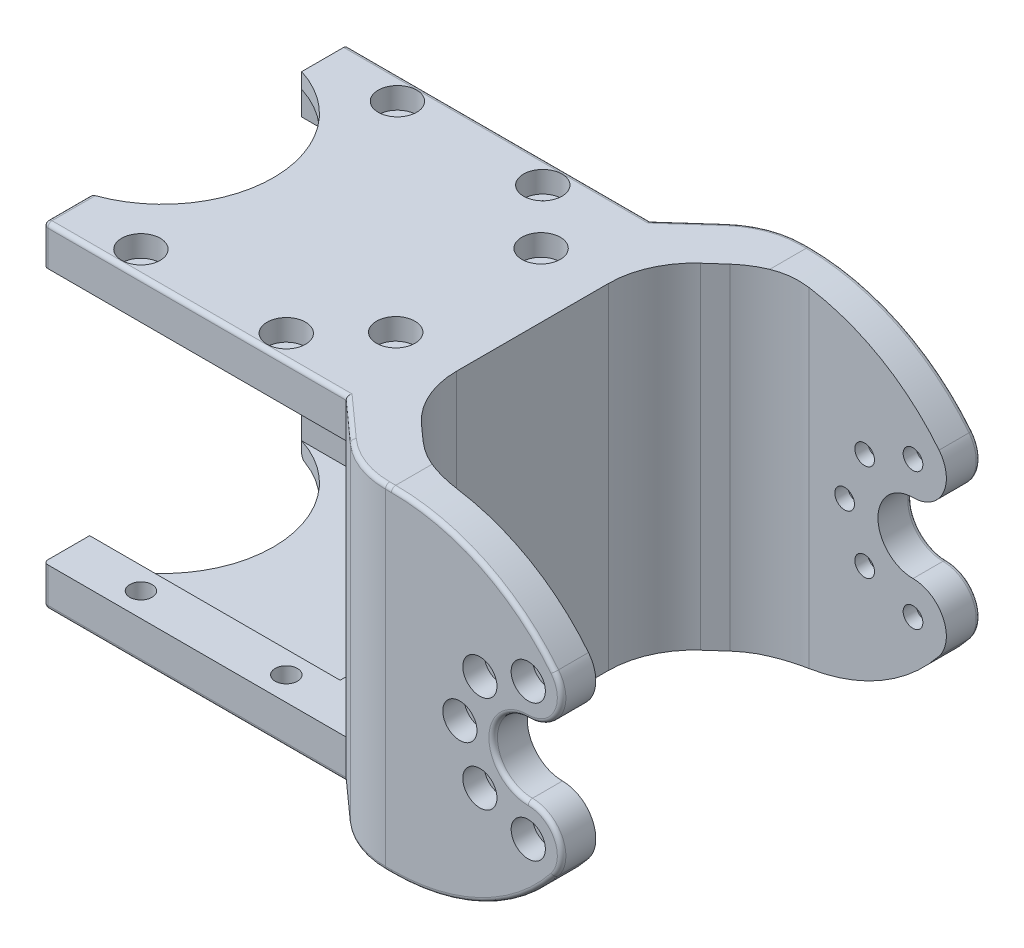
SolidWorks part; units mm, degrees
ref_plane "Front Plane" through (0, 0, 0) normal (0, 0, 1) x (1, 0, 0)
ref_plane "Top Plane" through (0, 0, 0) normal (0, 1, 0) x (1, 0, 0)
ref_plane "Right Plane" through (0, 0, 0) normal (1, 0, 0) x (0, 0, -1)
sketch "Sketch1" plane through (0, 0, 0) normal (0, 1, 0) x (1, 0, 0)
  line L0 (0, 0) -> (0, 15) construction
  line L1 (0, 15) -> (-4.5, 15) construction
  line L2 (0, 0) -> (12.5, 0) construction
  line L3 (-4.5, 12.4) -> (33.2, 12.4) construction
  line L4 (33.2, 12.4) -> (33.2, -12.4)
  line L5 (-4.5, 17.8) -> (38.3, 17.8) construction
  line L6 (38.3, 17.8) -> (38.3, -17.8)
  line L7 (33.2, 0) -> (38.3, 0) construction
  line L8 (-4.5, -12.4) -> (33.2, -12.4) construction
  line L9 (-4.5, -17.8) -> (38.3, -17.8) construction
  line L10 (-4.5, 17.8) -> (-12.2, 17.8) construction
  line L12 (-12.2, 12.4) -> (-4.5, 12.4) construction
  line L13 (-12.2, -12.4) -> (-4.5, -12.4) construction
  line L16 (-12.2, 12.4) -> (-12.2, -12.4) construction
  line L26 (3.9038, 12.4) -> (3.9038, 17.8)
  line L27 (3.9038, 17.8) -> (38.3, 17.8)
  line L28 (3.9038, -12.4) -> (3.9038, -17.8)
  line L29 (3.9038, -17.8) -> (38.3, -17.8)
  line L30 (3.9038, 12.4) -> (33.2, 12.4)
  line L31 (3.9038, -12.4) -> (33.2, -12.4)
  circle A0 centre (-4.5, 15) radius 1.3 construction
  circle A1 centre (12.5, 15) radius 1.3
  circle A2 centre (29.5, 15) radius 1.3
  circle A4 centre (29.5, -15) radius 1.3
  circle A5 centre (12.5, -15) radius 1.3
  circle A6 centre (-4.5, -15) radius 1.3 construction
  circle A8 centre (0, 0) radius 11 construction
  circle A9 centre (-4.5, 15) radius 2.25 construction
  arc A14 (3.9038, 12.4) -> (3.9038, -12.4) centre (0, 0) cw construction
  circle A15 centre (35.8, -8.5) radius 1.3
  circle A16 centre (35.8, 8.5) radius 1.3
  dimension "D4" = 2.6
  dimension "D12" = 22
  dimension "D13" = 4.5
  dimension "D16" = 6.5
  dimension "D15" = 6.3
  dimension "D14" = 13
  dimension "D1" = 15
  dimension "D2" = 4.5
  dimension "D3" = 17
  dimension "D6" = 2.6
  dimension "D7" = 34
  dimension "D8" = 3.7
  dimension "D9" = 2.8
  dimension "D10" = 5.1
  dimension "D11" = 7.7
  dimension "D5" = 3
extrude "Boss-Extrude1" add sketch "Sketch1" along normal blind 2.8
sketch "Sketch2" plane through (0, 2.8, 0) normal (0, 1, 0) x (1, 0, 0)
  line L0 (3.9038, -12.4) -> (3.9038, -17.8) construction
  line L1 (3.9038, -17.8) -> (38.3, -17.8) construction
  line L2 (38.3, 17.8) -> (38.3, -17.8) construction
  line L3 (3.9038, 17.8) -> (38.3, 17.8) construction
  line L4 (3.9038, 12.4) -> (3.9038, 17.8) construction
  line L5 (3.9038, -12.4) -> (3.9038, -17.8)
  line L6 (3.9038, -17.8) -> (38.3, -17.8)
  line L7 (38.3, 17.8) -> (38.3, -17.8)
  line L8 (3.9038, 17.8) -> (38.3, 17.8)
  line L9 (3.9038, 12.4) -> (3.9038, 17.8)
  arc A0 (3.9038, -12.4) -> (3.9038, 12.4) centre (0, 0) ccw construction
  arc A1 (3.9038, -12.4) -> (3.9038, 12.4) centre (0, 0) ccw
  circle A2 centre (12.5, -15) radius 1.3 construction
  circle A3 centre (29.5, -15) radius 1.3 construction
  circle A4 centre (35.8, -8.5) radius 1.3 construction
  circle A5 centre (35.8, 8.5) radius 1.3 construction
  circle A6 centre (29.5, 15) radius 1.3 construction
  circle A7 centre (12.5, 15) radius 1.3 construction
  circle A8 centre (12.5, -15) radius 1.3
  circle A9 centre (29.5, -15) radius 1.3
  circle A10 centre (35.8, -8.5) radius 1.3
  circle A11 centre (35.8, 8.5) radius 1.3
  circle A12 centre (29.5, 15) radius 1.3
  circle A13 centre (12.5, 15) radius 1.3
extrude "Boss-Extrude2" add sketch "Sketch2" along normal blind 1.8
sketch "Sketch3" plane through (0, 4.6, 0) normal (0, 1, 0) x (1, 0, 0)
  line L0 (0, 0) -> (38.3, 0) construction
  line L1 (38.3, -17.8) -> (38.3, 17.8) construction
  circle A0 centre (35.8, 8.5) radius 1.3 construction
  circle A1 centre (29.5, 15) radius 1.3 construction
  circle A2 centre (12.5, 15) radius 1.3 construction
  circle A3 centre (35.8, 8.5) radius 1.3 construction
  circle A4 centre (29.5, 15) radius 1.3 construction
  circle A5 centre (12.5, 15) radius 1.3 construction
  circle A6 centre (12.5, 15) radius 2.25
  circle A7 centre (29.5, 15) radius 2.25
  circle A8 centre (35.8, 8.5) radius 2.25
  circle A9 centre (35.8, -8.5) radius 2.25
  circle A10 centre (29.5, -15) radius 2.25
  circle A11 centre (12.5, -15) radius 2.25
  dimension "D1" = 4.5
extrude "Cut-Extrude1" cut sketch "Sketch3" against normal blind 2.5
sketch "Sketch4" plane through (38.3, 0, 0) normal (1, 0, 0) x (0, 0, -1)
  line L4 (-17.8, 0) -> (17.8, 0)
  line L5 (17.8, 0) -> (17.8, 4.6)
  line L6 (17.8, 4.6) -> (-17.8, 4.6)
  line L7 (-17.8, 4.6) -> (-17.8, 0)
  line L8 (-17.8, 0) -> (17.8, 0)
  line L9 (17.8, 0) -> (17.8, 4.6)
  line L10 (17.8, 4.6) -> (-17.8, 4.6)
  line L11 (-17.8, 4.6) -> (-17.8, 0)
  dimension "D1" = 0
extrude "Boss-Extrude3" add sketch "Sketch4" along normal blind 5
sketch "Sketch5" plane through (0, 0, 0) normal (0, -1, 0) x (1, 0, 0)
  line L0 (43.3, -17.8) -> (3.9038, -17.8) construction
  line L1 (43.3, 17.8) -> (39.3, 17.8)
  line L2 (43.3, 17.8) -> (43.3, -17.8)
  line L3 (43.3, -17.8) -> (39.3, -17.8)
  line L4 (39.3, 17.8) -> (39.3, -17.8)
  dimension "D1" = 4
extrude "Boss-Extrude4" add sketch "Sketch5" along normal blind 15
mirror "Mirror1" about plane through (0, -15, 0) normal (0, 1, 0) of bodies 133
sketch "Sketch6" plane through (0, 0, 0) normal (0, 0, 1) x (1, 0, 0)
  line L0 (43.3, -15) -> (67.3, -15) construction
  line L1 (43.3, 4.6) -> (43.3, -34.6) construction
  line L2 (0, 0) -> (0, -15) construction
  line L3 (0, -15) -> (43.3, -15) construction
  dimension "D1" = 24
ref_plane "Plane1" through (0, -15, 0) normal (0, 1, 0) x (1, 0, 0)
sketch "Sketch7" plane through (0, -15, 0) normal (0, 1, 0) x (1, 0, 0)
  line L0 (43.3, 0) -> (67.3, 0) construction
  line L1 (43.3, 0) -> (67.3, 0) construction
  line L2 (67.3, -20.5) -> (67.3, 20.5) construction
  point P5 (67.3, 0)
  dimension "D1" = 41
ref_plane "Plane2" through (0, 0, 20.5) normal (0, 0, 1) x (1, 0, 0)
sketch "Sketch8" plane through (0, 0, 20.5) normal (0, 0, 1) x (1, 0, 0)
  line L0 (43.3, -15) -> (67.3, -15) construction
  line L1 (51.3, -34.6) -> (51.3, 4.6)
  line L3 (43.3, 4.6) -> (43.3, -34.6) construction
  line L4 (43.3, 4.6) -> (43.3, -34.6) construction
  line L5 (43.3, -15) -> (67.3, -15) construction
  circle A0 centre (67.3, -15) radius 4.1 construction
  circle A1 centre (67.3, -7) radius 1.15
  circle A2 centre (61.6431, -9.3431) radius 1.15
  circle A3 centre (59.3, -15) radius 1.15
  circle A4 centre (61.6431, -20.6569) radius 1.15
  circle A5 centre (67.3, -23) radius 1.15
  arc A6 (67.3, -10.9) -> (67.3, -19.1) centre (67.3, -15) ccw
  arc A7 (67.3, -10.9) -> (70.3479, -4.5668) centre (67.3, -7) ccw
  arc A8 (51.3, 4.6) -> (70.3479, -4.5668) centre (51.3, -19.7734) cw
  arc A9 (67.3, -19.1) -> (70.3479, -25.4332) centre (67.3, -23) cw
  arc A10 (51.3, -34.6) -> (70.3479, -25.4332) centre (51.3, -10.2266) ccw
  point P15 (67.3, -15)
  point P22 (51.3, -15)
  dimension "D1" = 8.2
  dimension "D3" = 2.3
  dimension "D2" = 8
  dimension "D5" = 16
  dimension "D4" = 5
extrude "Boss-Extrude5" add sketch "Sketch8" along normal blind 4 separate body
sketch "Sketch10" plane through (0, 0, 17.8) normal (0, 0, 1) x (1, 0, 0)
  line L0 (39.3, -30) -> (39.3, 0) construction
  line L1 (39.3, -30) -> (39.3, 0) construction
  line L2 (3.9038, -34.6) -> (43.3, -34.6) construction
  line L3 (43.3, 4.6) -> (39.3, 4.6)
  line L4 (43.3, 4.6) -> (43.3, -34.6)
  line L5 (43.3, -34.6) -> (39.3, -34.6)
  line L6 (39.3, 4.6) -> (39.3, -34.6)
sketch "Sketch11" plane through (0, 4.6, 0) normal (0, 1, 0) x (1, 0, 0)
  line L0 (43.3, -13.3343) -> (39.3, -17.8)
  line L1 (43.3, 17.8) -> (43.3, -17.8) construction
  line L2 (3.9038, -17.8) -> (43.3, -17.8) construction
  line L3 (43.3, -13.3343) -> (51.3, -20.5)
  line L4 (39.3, -17.8) -> (46.7801, -24.5)
  line L5 (46.7801, -24.5) -> (51.3, -24.5)
  line L6 (51.3, -20.5) -> (51.3, -24.5)
  dimension "D1" = 4
extrude "Boss-Extrude7" add sketch "Sketch11" against normal up to surface (39.2 mm away)
fillet "Fillet1" radius 10 3 edges at (51.3, -15, 20.5) (43.3, -15, 13.3343) (46.7801, -15, 24.5)
mirror "Mirror6" about plane through (0, 0, 0) normal (0, 0, 1) of bodies 137
fillet "Fillet2" radius 0.5 32 edges at (41.6159, -34.6, -19.8744) (41.6159, 4.6, -19.8744) (47.0323, -34.6, -23.8404) (47.0323, 4.6, -23.8404) (50.9519, -34.6, -24.5) (61.8694, -32.1891, -24.5) (70.8142, -21.3088, -24.5) (63.2, -15, -24.5) (70.8142, -8.6912, -24.5) (61.8694, 2.1891, -24.5) (50.9519, 4.6, -24.5) (41.6159, -34.6, 19.8744) (41.6159, 4.6, 19.8744) (47.0323, -34.6, 23.8404) (50.9519, -34.6, 24.5) (61.8694, -32.1891, 24.5) (70.8142, -21.3088, 24.5) (63.2, -15, 24.5) (70.8142, -8.6912, 24.5) (61.8694, 2.1891, 24.5) (50.9519, 4.6, 24.5) (47.0323, 4.6, 23.8404) (3.9038, -34.6, -15.1) (3.9038, -32.3, -17.8) (21.6019, -34.6, -17.8) (21.6019, 4.6, -17.8) (3.9038, -34.6, 15.1) (3.9038, -32.3, 17.8) (21.6019, -34.6, 17.8) (3.9038, 2.3, 17.8) (3.9038, 4.6, 15.1) (21.6019, 4.6, 17.8)
sketch "Sketch12" plane through (0, 0, 24.5) normal (0, 0, 1) x (1, 0, 0)
  arc A0 (67.3, -10.4) -> (67.3, -19.6) centre (67.3, -15) ccw construction
  circle A1 centre (67.3, -23) radius 1.15 construction
  arc A2 (67.3, -10.4) -> (67.3, -19.6) centre (67.3, -15) ccw construction
  circle A3 centre (67.3, -23) radius 1.15 construction
  circle A4 centre (67.3, -23) radius 2
  circle A5 centre (61.6431, -20.6569) radius 2
  circle A6 centre (59.3, -15) radius 2
  circle A7 centre (61.6431, -9.3431) radius 2
  circle A8 centre (67.3, -7) radius 2
  point P17 (67.3, -15)
  dimension "D1" = 4
  dimension "D2" = 5
extrude "Cut-Extrude2" cut sketch "Sketch12" against normal blind 2.5
mirror "Mirror7" about plane through (0, 0, 0) normal (0, 0, 1) of "Cut-Extrude2"
